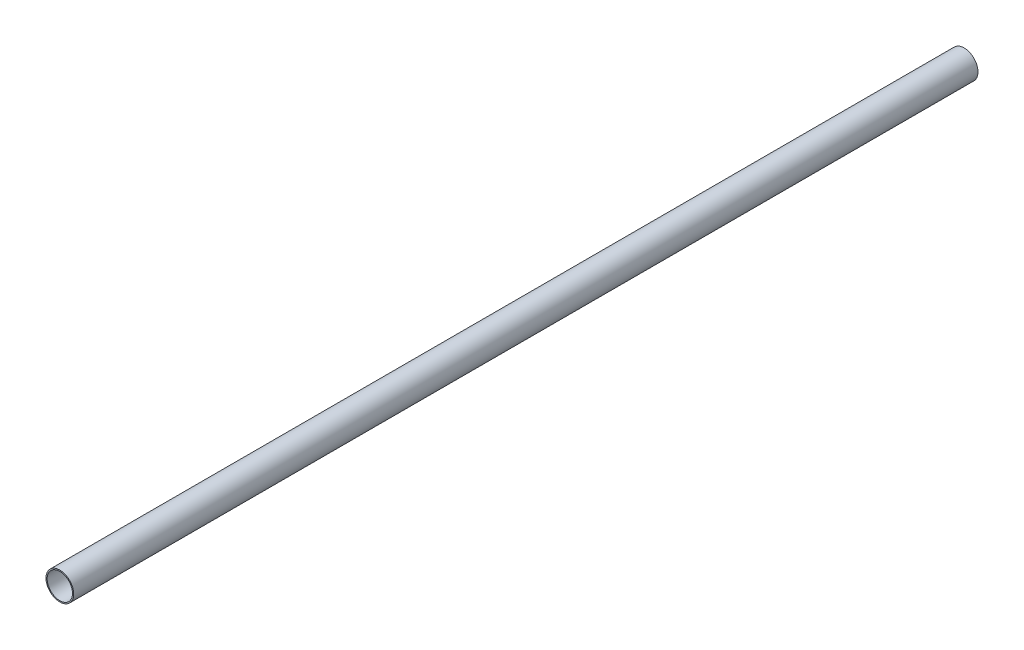
SolidWorks part; units mm, degrees
ref_plane "Front" through (0, 0, 0) normal (0, 0, 1) x (1, 0, 0)
ref_plane "Top" through (0, 0, 0) normal (0, 1, 0) x (1, 0, 0)
ref_plane "Side" through (0, 0, 0) normal (1, 0, 0) x (0, 0, -1)
sketch "PipeSketch" plane through (0, 0, 0) normal (0, 0, 1) x (1, 0, 0)
  circle A0 centre (0, 0) radius 84.074
  circle A1 centre (0, 0) radius 76.962
  dimension "OuterDiameter" = 168.148
  dimension "InnerDiameter" = 153.924
extrude "Extrusion" add sketch "PipeSketch" along normal blind 5486.4
sketch "FilterSketch" plane through (0, 0, 0) normal (0, 0, 1) x (1, 0, 0)
  circle A0 centre (0, 0) radius 76.2 construction
  dimension "NominalDiameter" = 152.4
